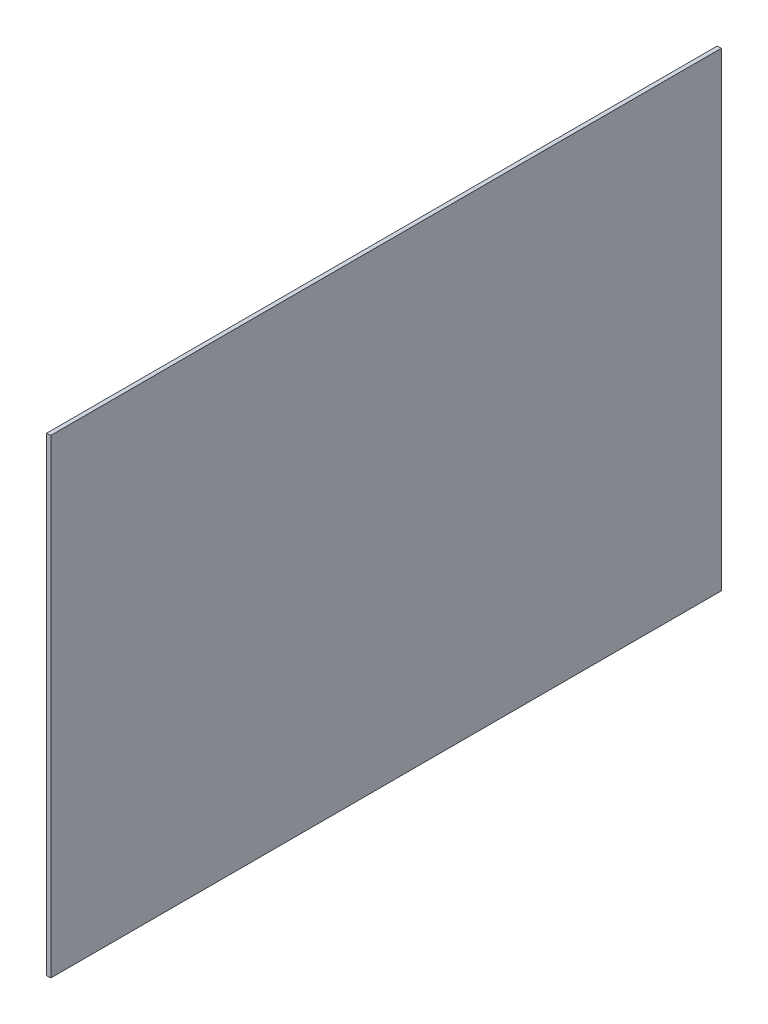
SolidWorks part; units mm, degrees
ref_plane "Front Plane" through (0, 0, 0) normal (0, 0, 1) x (1, 0, 0)
ref_plane "Top Plane" through (0, 0, 0) normal (0, 1, 0) x (1, 0, 0)
ref_plane "Right Plane" through (0, 0, 0) normal (1, 0, 0) x (0, 0, -1)
sketch "Sketch1" plane through (0, 0, 0) normal (1, 0, 0) x (0, 0, -1)
  line L0 (-250, 175.2053) -> (-250, -175.2053)
  line L1 (-250, -175.2053) -> (250, -175.2053)
  line L2 (250, -175.2053) -> (250, 175.2053)
  line L3 (250, 175.2053) -> (-250, 175.2053)
extrude "Boss-Extrude1" add sketch "Sketch1" along normal blind 3
